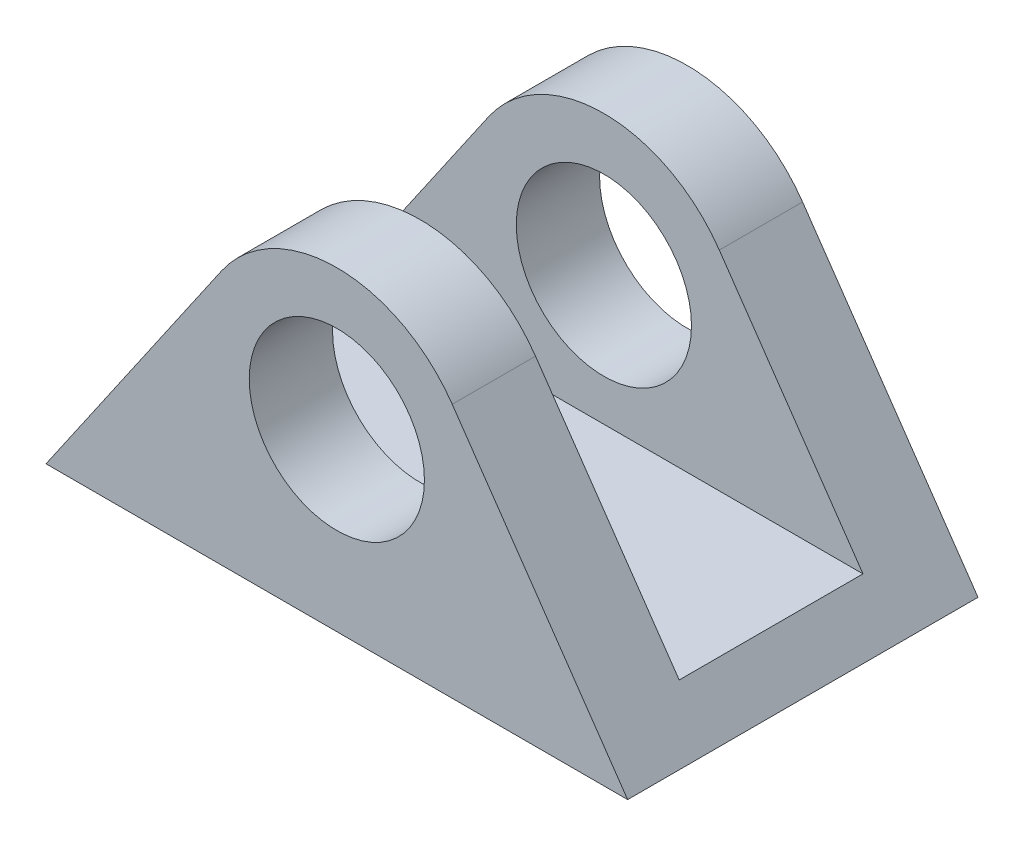
SolidWorks part; units mm, degrees
ref_plane "Front Plane" through (0, 0, 0) normal (0, 0, 1) x (1, 0, 0)
ref_plane "Top Plane" through (0, 0, 0) normal (0, 1, 0) x (1, 0, 0)
ref_plane "Right Plane" through (0, 0, 0) normal (1, 0, 0) x (0, 0, -1)
sketch "Sketch1" plane through (0, 0, 0) normal (0, 0, 1) x (1, 0, 0)
  line L0 (6.5884, 4.5379) -> (16.6018, -10)
  line L1 (16.6018, -10) -> (-16.6018, -10)
  line L2 (0, 0) -> (0, -10) construction
  line L3 (-6.5884, 4.5379) -> (-16.6018, -10)
  circle A0 centre (0, 0) radius 5
  circle A1 centre (0, 0) radius 8
  dimension "D1" = 10
  dimension "D3" = 10
  dimension "D2" = 3
extrude "Boss-Extrude1" add sketch "Sketch1" along normal blind 20
sketch "Sketch2" plane through (0, 0, 0) normal (1, 0, 0) x (0, 0, -1)
  line L0 (-10, 8) -> (-10, -3.4469) construction
  line L1 (0, 8) -> (-20, 8) construction
  line L3 (-15.2457, 11.9221) -> (-4.7543, 11.9221)
  line L4 (-15.2457, 11.9221) -> (-15.2457, -7.3689)
  line L5 (-15.2457, -7.3689) -> (-4.7543, -7.3689)
  line L6 (-4.7543, 11.9221) -> (-4.7543, -7.3689)
  line L7 (-15.2457, 11.9221) -> (-4.7543, -7.3689) construction
  line L8 (-15.2457, -7.3689) -> (-4.7543, 11.9221) construction
  point P4 (-10, 2.2766)
extrude "Cut-Extrude1" cut sketch "Sketch2" against normal through all and the other way through all
